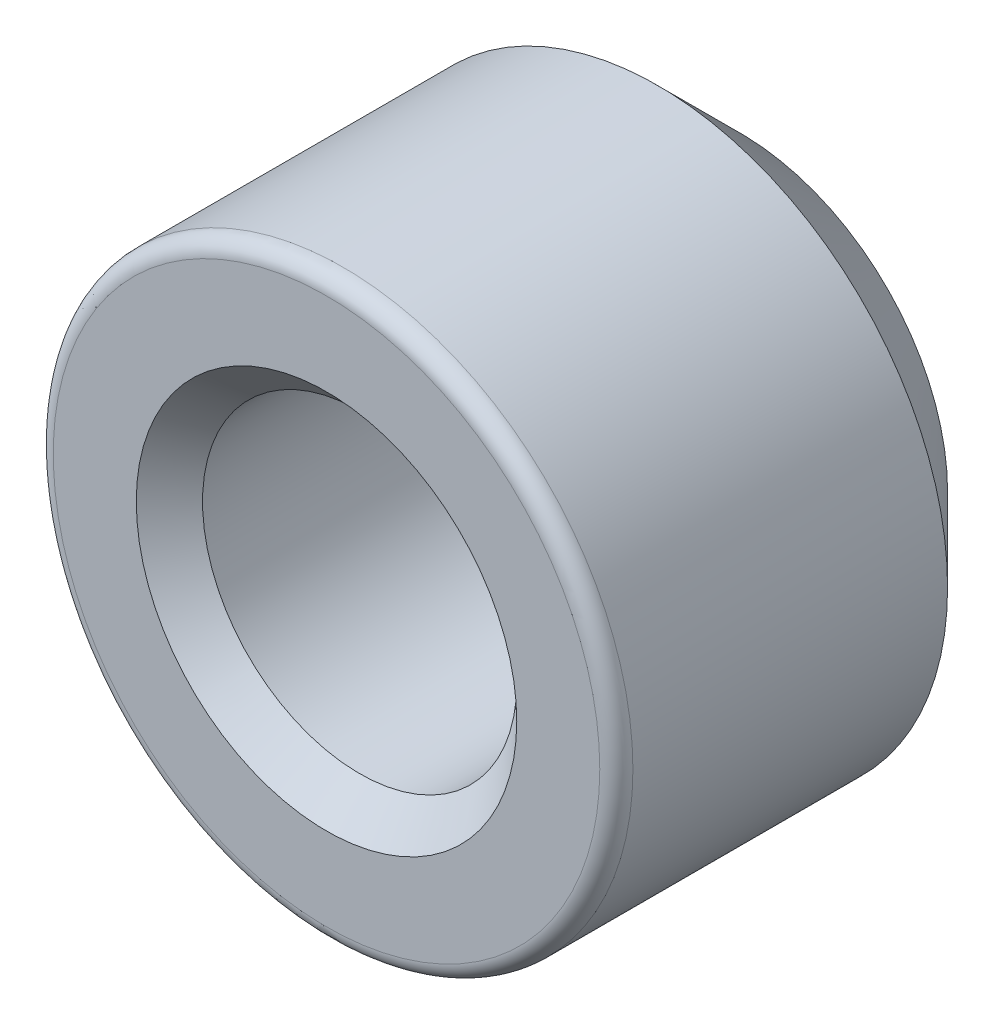
SolidWorks part; units mm, degrees
ref_plane "Front Plane" through (0, 0, 0) normal (0, 0, 1) x (1, 0, 0)
ref_plane "Top Plane" through (0, 0, 0) normal (0, 1, 0) x (1, 0, 0)
ref_plane "Right Plane" through (0, 0, 0) normal (1, 0, 0) x (0, 0, -1)
sketch "Sketch1" plane through (0, 0, 0) normal (0, 0, 1) x (1, 0, 0)
  circle A0 centre (0, 0) radius 17.5
  dimension "D1" = 35
extrude "Boss-Extrude1" add sketch "Sketch1" along normal mid plane 25
hole_wizard "1/2-14 NPSM Tapped Hole1" positions "Sketch2" profile "Sketch3" tap size "1/2-14 NPSM" standard "ANSI Inch"
sketch "Sketch2" plane through (0, 0, 12.5) normal (0, 0, 1) x (1, 0, 0)
  point P0 (0, 0)
sketch "Sketch3" plane through (0, 0, 12.5) normal (1, 0, 0) x (0, -1, 0)
  line L0 (0, 0) -> (0, 52.9494)
  line L1 (0, 52.9494) -> (9.4869, 47.2491)
  line L2 (9.4869, 47.2491) -> (9.4869, 0)
  line L5 (9.4869, 0) -> (0, 0)
  line L10 (0, 52.9494) -> (-9.4869, 47.2491) construction
  line L11 (0, -6.35) -> (0, 107.95) construction
  dimension "Tap Drill Dia." = 18.9738
  dimension "Tap Drill Depth" = 47.2491
  dimension "Drill Angle" = 118
cosmetic thread "Hole Thread1" parameters "D1"=40, "D2"=20.9042
chamfer "Chamfer1" distance 5 angle 45 1 edges at (17.5, 0, -12.5)
chamfer "Chamfer2" distance 2 angle 45 1 edges at (9.4869, 0, 12.5)
fillet "Fillet1" radius 1 1 edges at (17.5, 0, 12.5)
